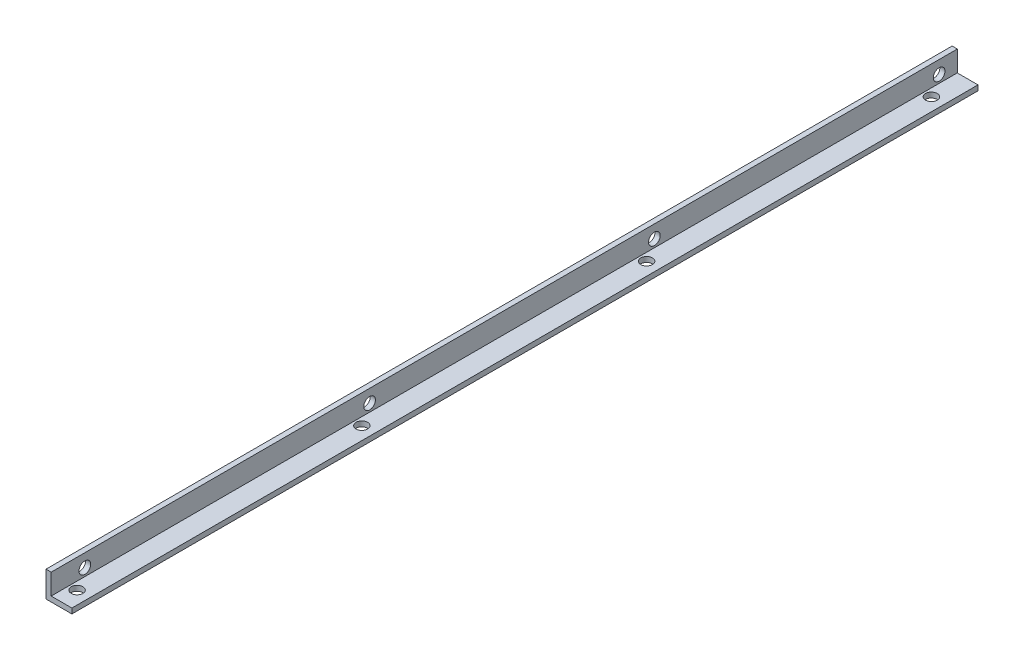
SolidWorks part; units mm, degrees
ref_plane "Спереди" through (0, 0, 0) normal (0, 0, 1) x (1, 0, 0)
ref_plane "Сверху" through (0, 0, 0) normal (0, 1, 0) x (1, 0, 0)
ref_plane "Справа" through (0, 0, 0) normal (1, 0, 0) x (0, 0, -1)
sketch "Эскиз1" plane through (0, 0, 0) normal (0, 0, 1) x (1, 0, 0)
  line L0 (0, 0) -> (0, 10)
  line L1 (0, 10) -> (2, 10)
  line L2 (2, 10) -> (2, 2)
  line L3 (2, 2) -> (10, 2)
  line L4 (10, 2) -> (10, 0)
  line L5 (10, 0) -> (0, 0)
  dimension "D1" = 10
  dimension "D2" = 10
  dimension "D3" = 2
  dimension "D4" = 2
extrude "Бобышка-Вытянуть1" add sketch "Эскиз1" along normal blind 350
sketch "Эскиз2" plane through (0, 0, 0) normal (-1, 0, 0) x (0, 0, 1)
  line L0 (350, 0) -> (0, 0) construction
  line L1 (350, 10) -> (350, 0) construction
  circle A0 centre (7, 5) radius 2.25
  circle A1 centre (117, 5) radius 2.25
  circle A2 centre (227, 5) radius 2.25
  circle A3 centre (337, 5) radius 2.25
  dimension "D1" = 110
  dimension "D2" = 110
  dimension "D3" = 110
  dimension "D5" = 13
  dimension "D6" = 4.5
  dimension "D4" = 5
extrude "Вырез-Вытянуть1" cut sketch "Эскиз2" against normal through all
sketch "Эскиз3" plane through (0, 0, 0) normal (0, -1, 0) x (1, 0, 0)
  line L0 (0, 350) -> (10, 350) construction
  line L1 (0, 350) -> (0, 0) construction
  circle A0 centre (5, 343) radius 2.25
  circle A1 centre (5, 233) radius 2.25
  circle A2 centre (5, 123) radius 2.25
  circle A3 centre (5, 13) radius 2.25
  dimension "D1" = 4.5
  dimension "D2" = 110
  dimension "D3" = 110
  dimension "D4" = 110
  dimension "D6" = 5
  dimension "D5" = 7
extrude "Вырез-Вытянуть2" cut sketch "Эскиз3" against normal up to next
